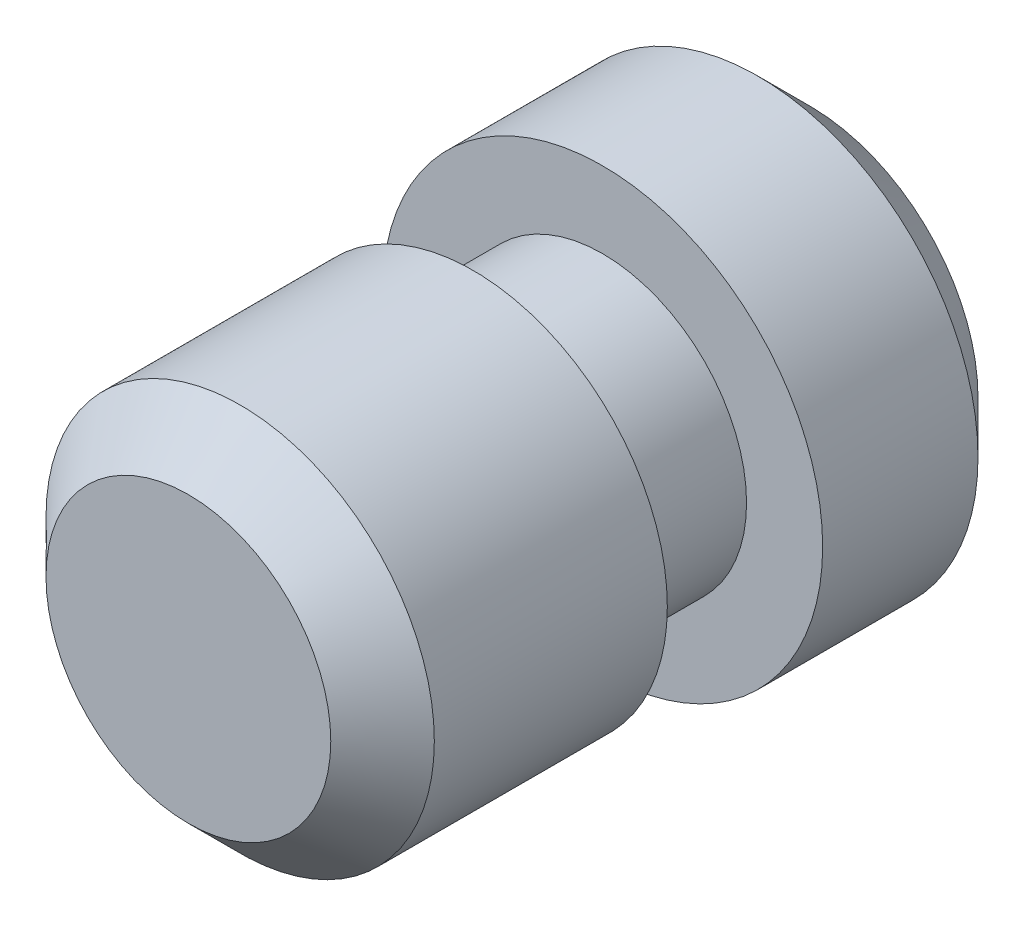
SolidWorks part; units mm, degrees
material "6063-T6"
ref_plane "Front" through (0, 0, 0) normal (0, 0, 1) x (1, 0, 0)
ref_plane "Top" through (0, 0, 0) normal (0, 1, 0) x (1, 0, 0)
ref_plane "Right" through (0, 0, 0) normal (1, 0, 0) x (0, 0, -1)
sketch "Sketch1" plane through (0, 0, 0) normal (0, 0, 1) x (1, 0, 0)
  circle A0 centre (0, 0) radius 5.3975
  dimension "D1" = 10.795
extrude "Boss-Extrude1" add sketch "Sketch1" along normal blind 5.08
sketch "Sketch3" plane through (0, 0, 5.08) normal (0, 0, 1) x (1, 0, 0)
  circle A0 centre (0, 0) radius 3.5306
  dimension "D1" = 7.0612
extrude "Boss-Extrude2" add sketch "Sketch3" along normal blind 3.175
sketch "Sketch4" plane through (0, 0, 8.255) normal (0, 0, 1) x (1, 0, 0)
  circle A0 centre (0, 0) radius 4.7625
  dimension "D1" = 9.525
extrude "Boss-Extrude3" add sketch "Sketch4" along normal blind 6.985
chamfer "Chamfer1" distance 1.27 angle 45 1 edges at (4.7625, 0, 15.24)
thread "Thread1" pitch 1.0583 start angle 0, offset 1.27, length 0, pitch 1.0583, diameter 9.525
ref_plane "Plane1" through (-4.7625, 0, 15.24) normal (0, -1, 0) x (-1, 0, 0)
sketch "Thread Profile1" plane through (-4.7625, 0, 15.24) normal (0, -1, 0) x (-1, 0, 0)
  line L0 (0, 0) -> (0, 1.0583) construction
  line L11 (0, 0) -> (0, 0.926)
  line L12 (0, 0.926) -> (-0.5728, 0.5953)
  line L13 (-0.5728, 0.5953) -> (-0.5728, 0.3307)
  line L15 (-0.5728, 0.3307) -> (0, 0)
  line L17 (-0.5728, 0.463) -> (0, 0.463) construction
  point P2 (0, 0)
  dimension "Pitch" = 1.0583
  dimension "Profile_Angle" = 60
  dimension "Profile_Land" = 0.2646
  dimension "Profile_Height" = 0.5728
chamfer "Chamfer2" distance 1.27 angle 45 1 edges at (5.3975, 0, 0)
